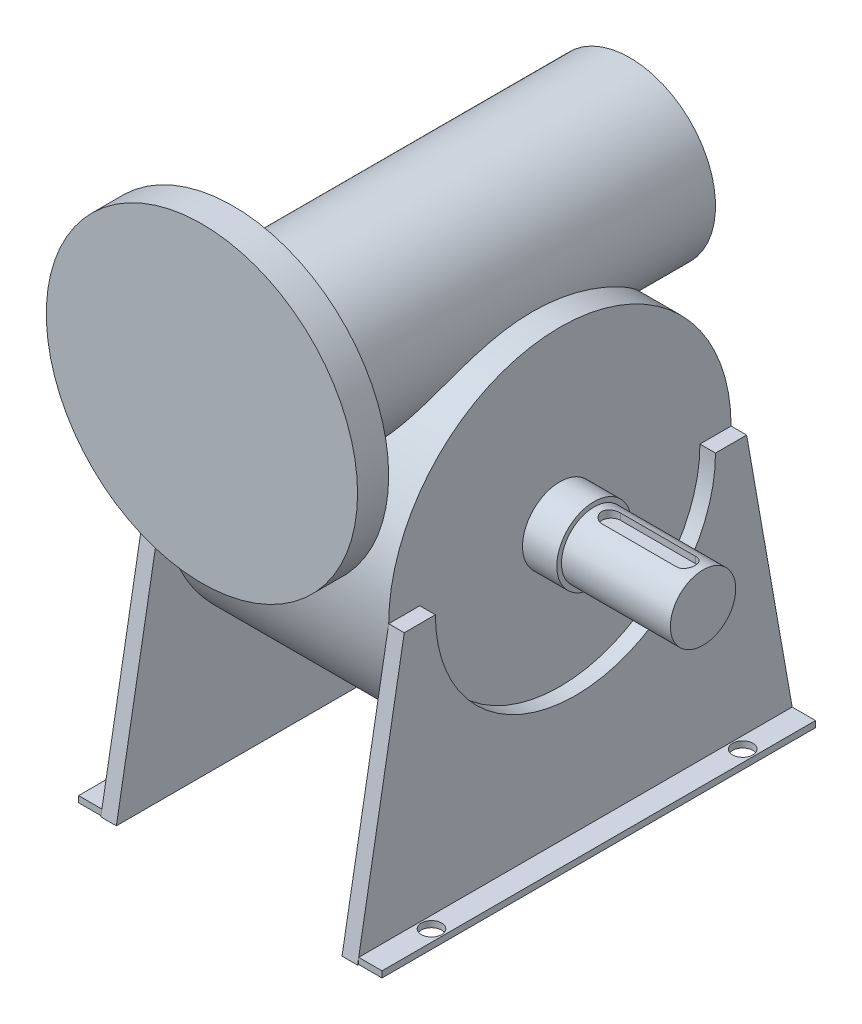
SolidWorks part; units mm, degrees
ref_plane "Front Plane" through (0, 0, 0) normal (0, 0, 1) x (1, 0, 0)
ref_plane "Top Plane" through (0, 0, 0) normal (0, 1, 0) x (1, 0, 0)
ref_plane "Right Plane" through (0, 0, 0) normal (1, 0, 0) x (0, 0, -1)
sketch "Sketch1" plane through (0, 0, 0) normal (0, 0, 1) x (1, 0, 0)
  circle A0 centre (0, 0) radius 100
  dimension "D1" = 200
extrude "Boss-Extrude1" add sketch "Sketch1" along normal blind 20
sketch "Sketch2" plane through (0, 0, 0) normal (0, 0, -1) x (-1, 0, 0)
  circle A0 centre (0, 0) radius 55
  dimension "D1" = 110
extrude "Boss-Extrude2" add sketch "Sketch2" along normal blind 255
sketch "Sketch3" plane through (0, 0, 0) normal (1, 0, 0) x (0, 0, -1)
  line L0 (255, -55) -> (255, 55) construction
  circle A0 centre (137.5, -110) radius 110
  dimension "D3" = 220
  dimension "D1" = 117.5
  dimension "D2" = 110
extrude "Boss-Extrude3" add sketch "Sketch3" along normal mid plane 145
sketch "Sketch4" plane through (72.5, 0, 0) normal (1, 0, 0) x (0, 0, -1)
  line L1 (-2.4756, -280) -> (137.5, -280)
  line L2 (137.5, -280) -> (137.5, -200)
  line L4 (-5.8842, -280.0208) -> (-2.4756, -280)
  line L5 (-2.4756, -280) -> (27.5, -110)
  line L7 (27.5, -110) -> (47.5, -110)
  circle A0 centre (137.5, -110) radius 110 construction
  arc A3 (47.5, -110) -> (137.5, -200) centre (137.5, -110) ccw
  circle M5 centre (137.5, -110) radius 110
  dimension "D1" = 170
  dimension "D2" = 90
  dimension "D3" = 10
  dimension "D4" = 0
extrude "Boss-Extrude4" add sketch "Sketch4" along normal blind 10 contours L5 L1 L2 M5 | A3 L7 L2 M5
mirror "Mirror1" about plane through (82.5, 0, -137.5) normal (0, 0, 1) of "Boss-Extrude4"
mirror "Mirror3" about plane through (0, 0, 0) normal (1, 0, 0) of "Boss-Extrude4"
mirror "Mirror4" about plane through (-82.5, 0, -137.5) normal (0, 0, -1) of "Mirror3"
sketch "Sketch5" plane through (72.5, 0, 0) normal (1, 0, 0) x (0, 0, -1)
  circle A0 centre (137.5, -110) radius 21
  arc A1 (247.5, -110) -> (27.5, -110) centre (137.5, -110) ccw construction
  dimension "D2" = 42
  dimension "D1" = 0
extrude "Boss-Extrude5" add sketch "Sketch5" along normal blind 92
sketch "Sketch7" plane through (72.5, 0, 0) normal (1, 0, 0) x (0, 0, -1)
  circle A0 centre (137.5, -110) radius 24
  dimension "D1" = 48
extrude "Boss-Extrude6" add sketch "Sketch7" along normal blind 22
ref_plane "Plane1" through (0, -89, 0) normal (0, 1, 0) x (1, 0, 0)
sketch "Sketch6" plane through (0, -89, 0) normal (0, 1, 0) x (1, 0, 0)
  line L0 (105.5, 143.5) -> (129.5, 143.5)
  line L1 (129.5, 143.5) -> (129.5, 131.5)
  line L2 (129.5, 131.5) -> (105.5, 131.5)
  line L3 (164.5, 158.5) -> (94.5, 158.5) construction
  line L5 (164.5, 116.5) -> (164.5, 158.5) construction
  arc A0 (105.5, 143.5) -> (105.5, 131.5) centre (105.5, 137.5) ccw
  dimension "D3" = 21
  dimension "D1" = 12
  dimension "D2" = 24
  dimension "D4" = 35
extrude "Cut-Extrude1" cut sketch "Sketch6" against normal blind 5
mirror "Mirror5" about plane through (129.5, -94, -143.5) normal (1, 0, 0) of "Cut-Extrude1"
sketch "Sketch8" plane through (82.5, 0, 0) normal (1, 0, 0) x (0, 0, -1)
  line L0 (-2.4756, -280) -> (27.5, -110) construction
  line L1 (-1.7703, -276) -> (276.7703, -276)
  line L2 (-1.7703, -276) -> (-1.7703, -280)
  line L3 (-1.7703, -280) -> (276.7703, -280)
  line L4 (276.7703, -276) -> (276.7703, -280)
  line L5 (-2.4756, -280) -> (277.4756, -280) construction
  line L6 (277.4756, -280) -> (247.5, -110) construction
  dimension "D1" = 4
extrude "Boss-Extrude7" add sketch "Sketch8" along normal blind 15
sketch "Sketch9" plane through (0, -280, 0) normal (0, -1, 0) x (1, 0, 0)
  line L2 (164.5, -137.5) -> (-132.8263, -137.5) construction
  line L3 (164.5, -158.5) -> (164.5, -116.5) construction
  point P0 (90, -37.5)
  point P1 (90, -237.5)
  dimension "D1" = 90
  dimension "D2" = 200
hole_wizard "Ø13.0 (13) Diameter Hole1" positions "Sketch12" profile "Sketch14" hole size "Ø13.0" standard "ISO" end condition through all
sketch "Sketch12" plane through (0, -280, 0) normal (0, -1, 0) x (-1, 0, 0)
  point P0 (-90, 37.5)
  point P4 (-90, 237.5)
sketch "Sketch14" plane through (90, -280, -37.5) normal (1, 0, 0) x (0, 0, -1)
  line L0 (0, 0) -> (0, 380)
  line L1 (0, 380) -> (6.5, 380)
  line L2 (6.5, 380) -> (6.5, 0)
  line L5 (6.5, 0) -> (0, 0)
  line L11 (0, -6.35) -> (0, 107.95) construction
  dimension "Thru Hole Dia." = 13
  dimension "Thru Hole Depth" = 380
mirror "Mirror8" about plane through (0, 0, 0) normal (1, 0, 0) of "Ø13.0 (13) Diameter Hole1", "Boss-Extrude7"
